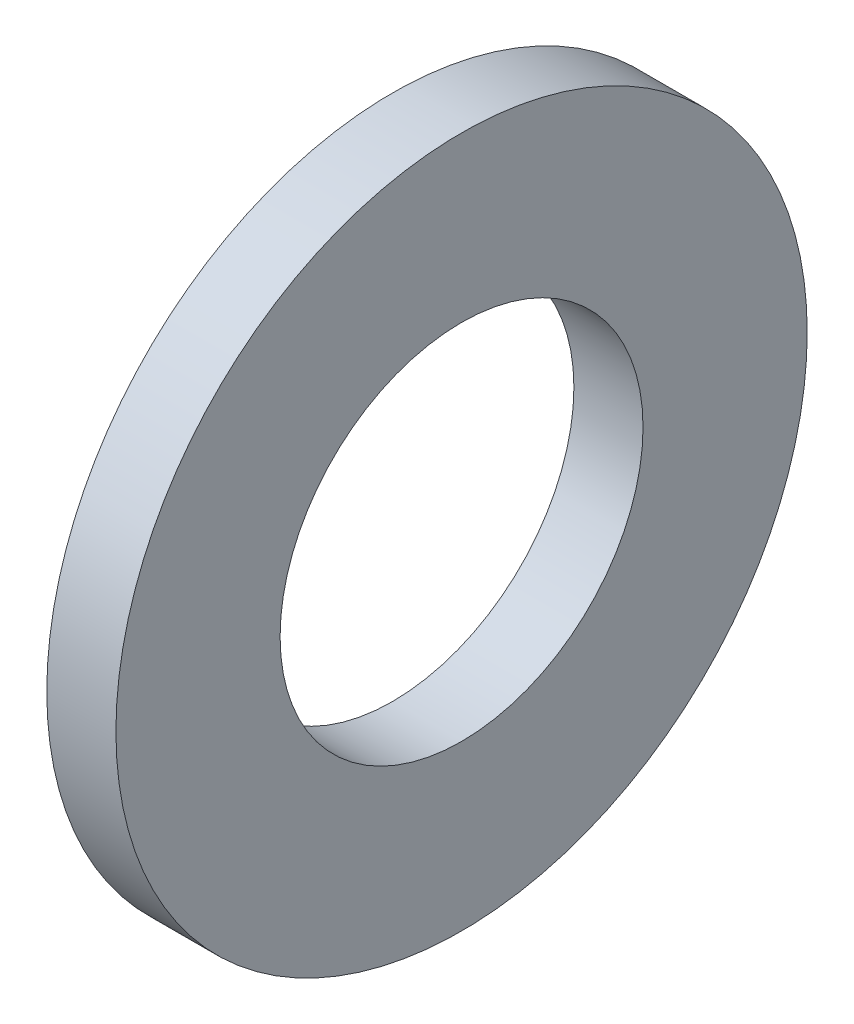
SolidWorks part; units mm, degrees
ref_plane "Plane1" through (0, 0, 0) normal (0, 0, 1) x (1, 0, 0)
ref_plane "Plane2" through (0, 0, 0) normal (0, 1, 0) x (1, 0, 0)
ref_plane "Plane3" through (0, 0, 0) normal (1, 0, 0) x (0, 0, -1)
sketch "Sketch1" plane through (0, 0, 0) normal (0, 0, 1) x (1, 0, 0)
  line L0 (-34.925, 0) -> (9.525, 0) construction
  line L1 (0, 4.2) -> (0, 8)
  line L2 (0, 8) -> (-1.6, 8)
  line L3 (-1.6, 8) -> (-1.6, 4.2)
  line L4 (-1.6, 4.2) -> (0, 4.2)
  dimension "Thickness" = 1.6
  dimension "Inside_dia" = 8.4
  dimension "Outside_dia" = 16
revolve "Base-Revolve" add sketch "Sketch1" angle 360 about L0
chamfer "ODChamfer" [suppressed] distance 0.4 angle 45
equation "\"D1@ODChamfer\" =  \"Thickness@Sketch1\" * 0.25"
